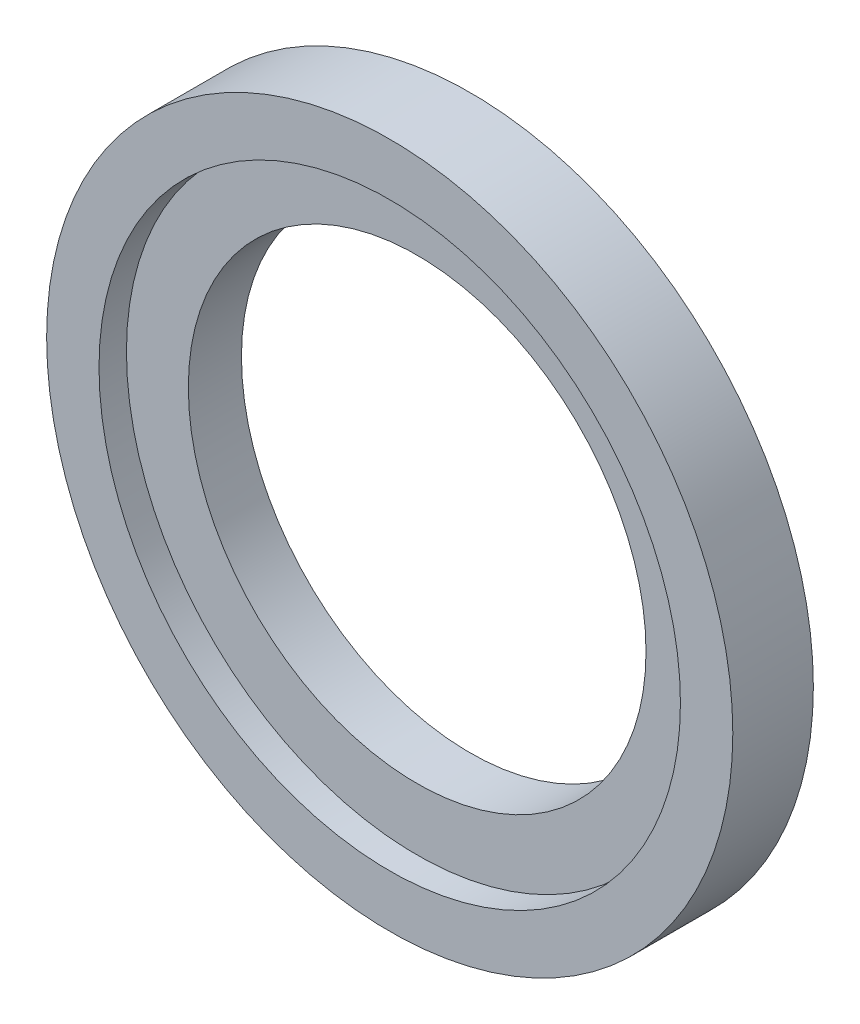
SolidWorks part; units mm, degrees
ref_plane "Front Plane" through (0, 0, 0) normal (0, 0, 1) x (1, 0, 0)
ref_plane "Top Plane" through (0, 0, 0) normal (0, 1, 0) x (1, 0, 0)
ref_plane "Right Plane" through (0, 0, 0) normal (1, 0, 0) x (0, 0, -1)
sketch "Sketch1" plane through (0, 0, 0) normal (0, 0, 1) x (1, 0, 0)
  circle A0 centre (0, 0) radius 25
  dimension "D1" = 50
extrude "Boss-Extrude1" add sketch "Sketch1" along normal blind 5.87
sketch "Sketch2" plane through (0, 0, 0) normal (0, 0, -1) x (-1, 0, 0)
  circle A0 centre (0, 0) radius 16.675
  dimension "D1" = 33.35
extrude "Cut-Extrude1" cut sketch "Sketch2" against normal through all
sketch "Sketch3" plane through (0, 0, 5.87) normal (0, 0, 1) x (1, 0, 0)
  circle A0 centre (0, 0) radius 21.1841
  dimension "D1" = 42.3683
extrude "Cut-Extrude2" cut sketch "Sketch3" against normal blind 2
